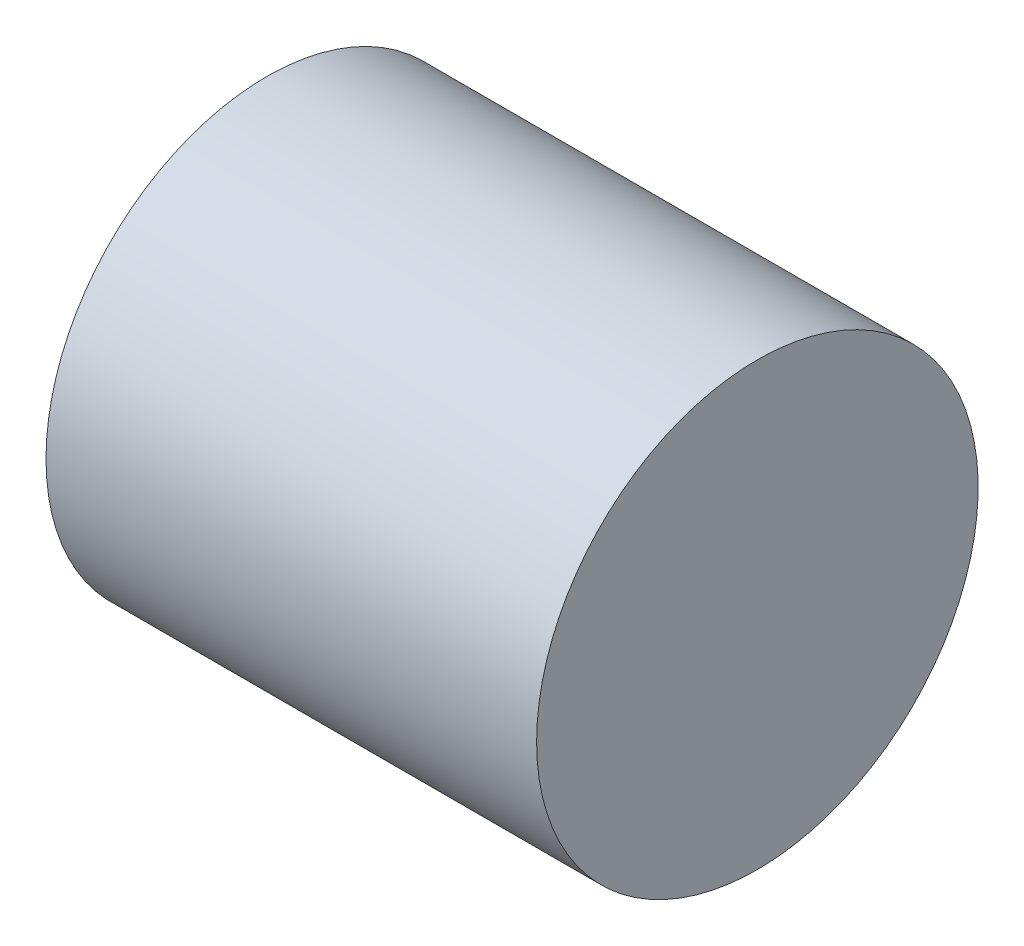
SolidWorks part; units mm, degrees
material "1023 al carbonio, lamiera (SS)"
ref_plane "Piano frontale" through (0, 0, 0) normal (0, 0, 1) x (1, 0, 0)
ref_plane "Piano superiore" through (0, 0, 0) normal (0, 1, 0) x (1, 0, 0)
ref_plane "Piano destro" through (0, 0, 0) normal (1, 0, 0) x (0, 0, -1)
sketch "Schizzo1" plane through (0, 0, 0) normal (0, 0, 1) x (1, 0, 0)
  line L1 (0, 0) -> (40, 0)
  line L2 (0, 0) -> (0, 18)
  line L3 (0, 18) -> (40, 18)
  line L4 (40, 0) -> (40, 18)
  dimension "D1" = 18
  dimension "D2" = 40
revolve "Rivoluzione1" add sketch "Schizzo1" angle 360 about L3
